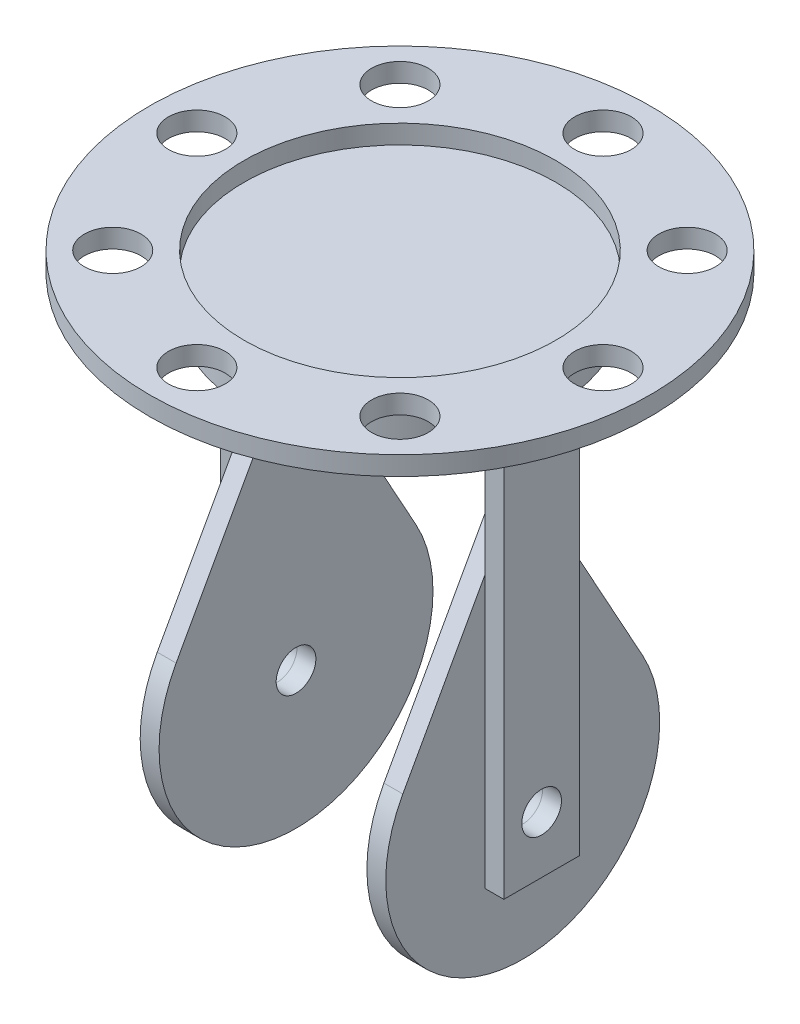
SolidWorks part; units mm, degrees
other "DetailItem2"
other "DetailItem3"
other "DetailItem4"
other "DetailItem5"
other "DetailItem6"
other "DetailItem7"
other "DetailItem8"
other "DetailItem9"
other "DetailItem10"
other "Weld Folder"
other "Weld Bead2"
other "Weld Bead3"
other "Weld Bead4"
other "Weld Bead5"
other "Weld Bead6"
other "Weld Bead9"
other "Weld Bead10"
other "Weld Bead8"
other "Weld Bead7"
ref_plane "Front Plane" through (0, 0, 0) normal (0, 0, 1) x (1, 0, 0)
ref_plane "Top Plane" through (0, 0, 0) normal (0, 1, 0) x (1, 0, 0)
ref_plane "Right Plane" through (0, 0, 0) normal (1, 0, 0) x (0, 0, -1)
sketch "Sketch1" plane through (0, 0, 0) normal (1, 0, 0) x (0, 0, -1)
  line L0 (-63.4691, 35.0417) -> (-8.7544, 134.1437)
  line L1 (8.7544, 134.1437) -> (63.4691, 35.0417)
  circle A0 centre (0, 0) radius 10.5
  circle A1 centre (0, 0) radius 72.5
  arc A2 (-8.7544, 134.1437) -> (8.7544, 134.1437) centre (0, 129.3103) cw
  point P10 (0, 150)
  dimension "D2" = 21
  dimension "D3" = 145
  dimension "D4" = 10
  dimension "D1" = 150
extrude "Boss-Extrude1" add sketch "Sketch1" against normal blind 10 contours A2 L0 A1 L1 | A1 A0
sketch "Sketch2" plane through (0, 0, 0) normal (1, 0, 0) x (0, 0, -1)
  line L1 (-20, -30) -> (20, -30)
  line L2 (-20, -30) -> (-20, 190)
  line L3 (-20, 190) -> (20, 190)
  line L4 (20, -30) -> (20, 190)
  circle A0 centre (0, 0) radius 10.5 construction
  circle A1 centre (0, 0) radius 10.5
  point P4 (0, -30)
  dimension "D1" = 20
  dimension "D2" = 220
  dimension "D3" = 30
extrude "Boss-Extrude2" add sketch "Sketch2" along normal blind 10 separate body
sketch "Sketch3" plane through (0, 0, 0) normal (-1, 0, 0) x (0, 0, 1)
  line L0 (20, 190) -> (20, -30) construction
  line L1 (-20, 190) -> (20, 190)
  line L2 (-20, 190) -> (-20, 180)
  line L3 (-20, 180) -> (20, 180)
  line L4 (20, 190) -> (20, 180)
  dimension "D1" = 10
extrude "Boss-Extrude3" add sketch "Sketch3" along normal blind 65
fillet "Fillet1" radius 10 1 edges at (0, 180, 0)
fillet "Fillet2" radius 20 1 edges at (10, 190, 0)
ref_plane "Plane1" through (-65, 0, 0) normal (-1, 0, 0) x (0, 0, 1)
mirror "Mirror1" about plane through (-65, 0, 0) normal (-1, 0, 0) of bodies 101 103
sketch "Sketch4" plane through (0, 190, 0) normal (0, 1, 0) x (1, 0, 0)
  line L0 (-65, 5.5) -> (-65, -5.5) construction
  circle A0 centre (-65, 0) radius 82.5
  dimension "D1" = 165
extrude "Boss-Extrude4" add sketch "Sketch4" along normal blind 20 separate body
sketch "Sketch5" plane through (0, 210, 0) normal (0, 1, 0) x (1, 0, 0)
  circle A0 centre (-65, 0) radius 132.5
  circle A1 centre (-65, 0) radius 82.5
  circle A2 centre (-65, 0) radius 82.5
  dimension "D1" = 0
  dimension "D2" = 50
extrude "Boss-Extrude5" add sketch "Sketch5" along normal blind 10 separate body
sketch "Sketch6" plane through (0, 210, 0) normal (0, -1, 0) x (1, 0, 0)
  line L0 (-65, 82.5) -> (-65, 132.5) construction
  circle A0 centre (-65, 107.5) radius 15
  circle A1 centre (-65, 0) radius 82.5 construction
  circle A2 centre (-65, 0) radius 82.5 construction
  circle A3 centre (-65, 0) radius 132.5 construction
  circle A4 centre (11.014, 76.014) radius 15
  circle A5 centre (42.5, 0) radius 15
  circle A6 centre (11.014, -76.014) radius 15
  circle A7 centre (-65, -107.5) radius 15
  circle A8 centre (-141.014, -76.014) radius 15
  circle A9 centre (-172.5, 0) radius 15
  circle A10 centre (-141.014, 76.014) radius 15
  point P11 (-65, 107.5)
  point P12 (0, 0)
  point P29 (-65, 0)
  dimension "D1" = 30
  dimension "D2" = 8
extrude "Cut-Extrude1" cut sketch "Sketch6" against normal through all
